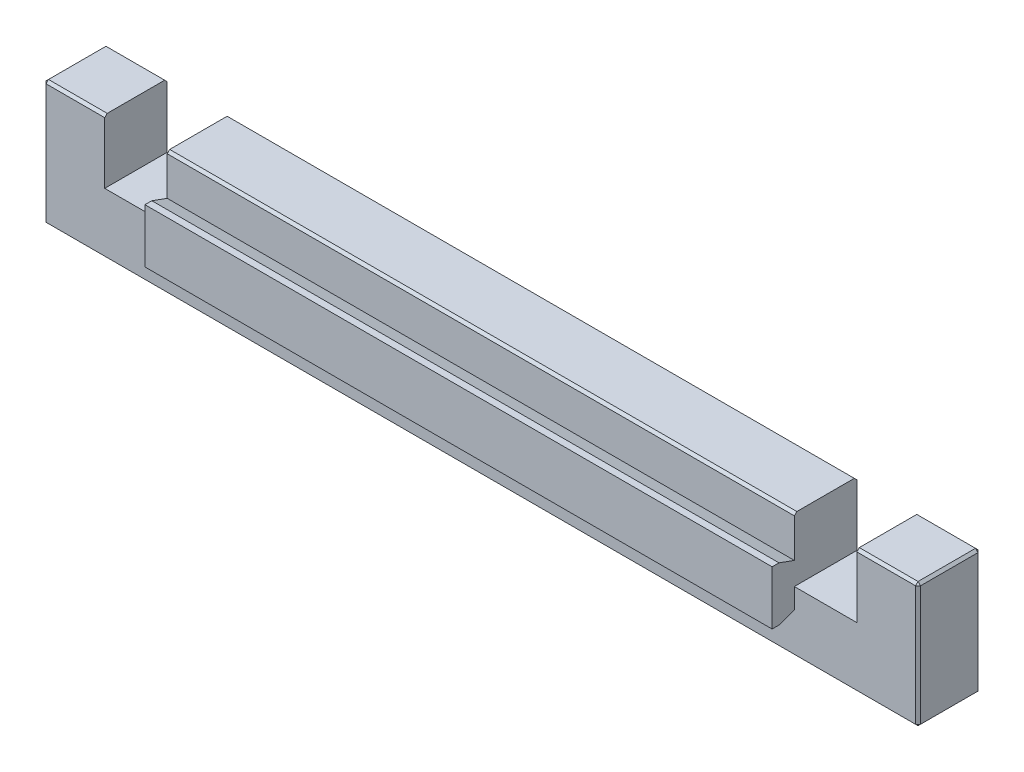
SolidWorks part; units mm, degrees
material "PETG"
ref_plane "Front Plane" through (0, 0, 0) normal (0, 0, 1) x (1, 0, 0)
ref_plane "Top Plane" through (0, 0, 0) normal (0, 1, 0) x (1, 0, 0)
ref_plane "Right Plane" through (0, 0, 0) normal (1, 0, 0) x (0, 0, -1)
sketch "Sketch2" plane through (0, 0, 0) normal (0, 0, 1) x (1, 0, 0)
  line L1 (-35, 5) -> (-30, 5)
  line L2 (-35, 5) -> (-35, -5)
  line L3 (-35, -5) -> (35, -5)
  line L4 (35, 5) -> (35, -5)
  line L5 (0, 6.2171) -> (0, -5) construction
  line L7 (-30, 5) -> (-30, 0)
  line L8 (-30, 0) -> (-25.2, 0)
  line L9 (-25.2, 5) -> (-25.2, 0)
  line L10 (30, 5) -> (30, 0)
  line L11 (30, 0) -> (25.2, 0)
  line L12 (25.2, 5) -> (25.2, 0)
  line L13 (-25.2, 5) -> (25.2, 5)
  line L14 (30, 5) -> (35, 5)
  line L15 (0, -5.5) -> (0, 5.5) construction
  point P14 (-35, 0)
  dimension "D1" = 10
  dimension "D2" = 70
  dimension "D3" = 4.8
  dimension "D4" = 5
  dimension "D5" = 5
extrude "Boss-Extrude1" add sketch "Sketch2" along normal blind 5
other "Move Face1" face at (-30, 2.5, 2.5) face at (-25.2, 2.5, 2.5) face at (-27.6, 0, 2.5) face at (30, 2.5, 2.5) face at (27.6, 0, 2.5) face at (25.2, 2.5, 2.5) parameters "D1"=0.1
sketch "Sketch3" plane through (0, 0, 0) normal (1, 0, 0) x (0, 0, -1)
  line L0 (-5, 1.816) -> (-6.8794, 2.5)
  line L1 (-6.8794, 2.5) -> (-6.8794, -2.5)
  line L2 (-6.8794, -2.5) -> (-5, -1.816)
  line L6 (-5, 1.816) -> (-5, -1.816)
  line L11 (0, -5) -> (0, 5)
  line L12 (0, 5) -> (-5, 5)
  line L13 (-5, 5) -> (-5, -5)
  line L14 (-5, -5) -> (0, -5)
  line L15 (0, -5) -> (0, 5) construction
  line L16 (0, 5) -> (-5, 5) construction
  line L17 (-5, 5) -> (-5, -5) construction
  line L18 (-5, -5) -> (0, -5) construction
  point P6 (-6.8794, 0)
  dimension "D5" = 2
  dimension "D2" = 5
  dimension "D1" = 110
  dimension "D4" = 5
  dimension "D6" = 0
extrude "Boss-Extrude2" add sketch "Sketch3" along normal up to surface and the other way up to surface up to face at (25.1, 2.45, 2.5) other way up to face at (-25.1, 2.45, 2.5)
other "Move Face2" parameters "D1"=0.1
sketch "Sketch4" plane through (25.1, 0, 0) normal (1, 0, 0) x (0, 0, -1)
  line L0 (-5, -0.1) -> (-5, 1.7095)
  line L1 (-6.7794, -2.1572) -> (-6.7794, 2.1572)
  line L2 (-6.7794, 2.1572) -> (-6.2299, 2.1572)
  line L3 (-6.7794, -2.1572) -> (-6.2299, -2.1572)
  line L8 (0, -0.1) -> (0, 5)
  line L9 (0, 5) -> (-5, 5)
  line L10 (-5, 5) -> (-5, 1.7095)
  line L11 (-5, 1.7095) -> (-6.7794, 2.3572)
  line L12 (-6.7794, 2.3572) -> (-6.7794, -2.3572)
  line L13 (-6.7794, -2.3572) -> (-5, -1.7095)
  line L14 (-5, -1.7095) -> (-5, -0.1)
  line L15 (-5, -0.1) -> (0, -0.1)
  line L16 (0, -0.1) -> (0, 5)
  line L17 (0, 5) -> (-5, 5)
  line L18 (-5, 5) -> (-5, 1.7095)
  line L19 (-5, 1.7095) -> (-6.7794, 2.3572)
  line L20 (-6.7794, 2.3572) -> (-6.7794, -2.3572)
  line L21 (-6.7794, -2.3572) -> (-5, -1.7095)
  line L22 (-5, -1.7095) -> (-5, -0.1)
  line L23 (-5, -0.1) -> (0, -0.1)
  point P8 (-6.7794, 0)
  point P12 (-6.2299, -2.1572)
  line M12 (-5, 1.7095) -> (-6.7794, 2.3572)
  line M13 (-6.7794, 2.3572) -> (-6.7794, -2.3572)
  line M14 (-6.7794, -2.3572) -> (-5, -1.7095)
  dimension "D2" = 0.2
  dimension "D1" = 0
extrude "Cut-Extrude1" cut sketch "Sketch4" against normal through all contours L2 M13 M12 | L3 M13 M14
chamfer "Chamfer1" distance 0.2 angle 45 16 edges at (0, 5, 0) (0, 5, 5) (35, -5, 2.5) (-35, -5, 2.5) (0, -5, 5) (-32.55, 5, 5) (-32.55, 5, 0) (-35, 0, 5) (-35, 5, 2.5) (-35, 0, 0) (0, -5, 0) (32.55, 5, 5) (35, 0, 5) (35, 5, 2.5) (32.55, 5, 0) (35, 0, 0)
equation "\"D3@Sketch3\"=\"D1@Sketch3\""
